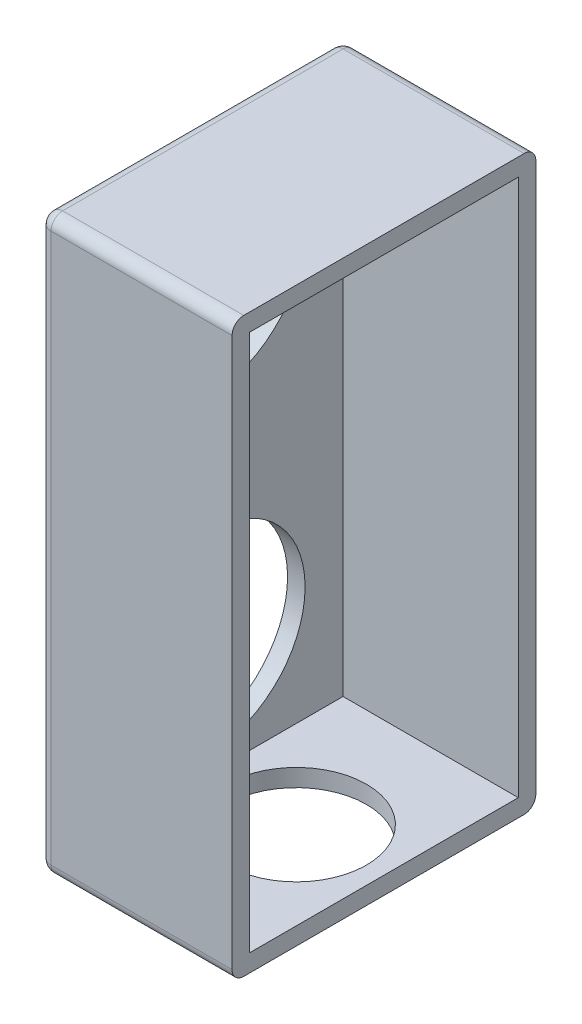
SolidWorks part; units mm, degrees
ref_plane "前视基准面" through (0, 0, 0) normal (0, 0, 1) x (1, 0, 0)
ref_plane "上视基准面" through (0, 0, 0) normal (0, 1, 0) x (1, 0, 0)
ref_plane "右视基准面" through (0, 0, 0) normal (1, 0, 0) x (0, 0, -1)
other "Configuration Table"
sketch "草图1" plane through (0, 0, 0) normal (0, 1, 0) x (1, 0, 0)
  line L1 (7.5, -11.5) -> (-7.5, -11.5)
  line L2 (7.5, -11.5) -> (7.5, 11.5)
  line L3 (7.5, 11.5) -> (-7.5, 11.5)
  line L4 (-7.5, -11.5) -> (-7.5, 11.5)
  line L5 (7.5, -11.5) -> (-7.5, 11.5) construction
  line L6 (7.5, 11.5) -> (-7.5, -11.5) construction
  point P0 (0, 0)
  dimension "D1" = 23
  dimension "D2" = 15
extrude "凸台-拉伸1" add sketch "草图1" along normal blind 46
ref_plane "基准面1" through (0, 0, 0) normal (0, -1, 0) x (-1, 0, 0)
sketch "草图2" plane through (0, 0, 0) normal (0, -1, 0) x (-1, 0, 0)
  circle A0 centre (0, 0) radius 6
shell "抽壳1" thickness 1.5
extrude "切除-拉伸4" cut sketch "草图2" along normal blind 1.5
ref_plane "基准面2" through (-9, 0, 0) normal (-1, 0, 0) x (0, 0, 1)
sketch "草图3" plane through (-9, 0, 0) normal (-1, 0, 0) x (0, 0, 1)
  line L0 (13, 23) -> (-13, 23) construction
  line L1 (13, 47.5) -> (13, -1.5) construction
  line L2 (-13, 47.5) -> (-13, -1.5) construction
  line L3 (0, 47.5) -> (0, -1.5) construction
  line L4 (-13, 47.5) -> (13, 47.5) construction
  line L5 (-13, -1.5) -> (13, -1.5) construction
  line L6 (5.2537, 28) -> (-4.4001, 28) construction
  line L7 (5.2537, 18) -> (-3.777, 18) construction
  circle A0 centre (0, 36.25) radius 8.25
  circle A1 centre (0, 9.75) radius 8.25
  dimension "D3" = 16.5
  dimension "D1" = 5
  dimension "D2" = 5
extrude "切除-拉伸5" cut sketch "草图3" against normal blind 1.5
fillet "圆角2" radius 1 8 edges at (-0.75, -1.5, 13) (-9, 23, 13) (-0.75, 47.5, 13) (-9, 47.5, 0) (-0.75, 47.5, -13) (-9, -1.5, 0) (-0.75, -1.5, -13) (-9, 23, -13)
